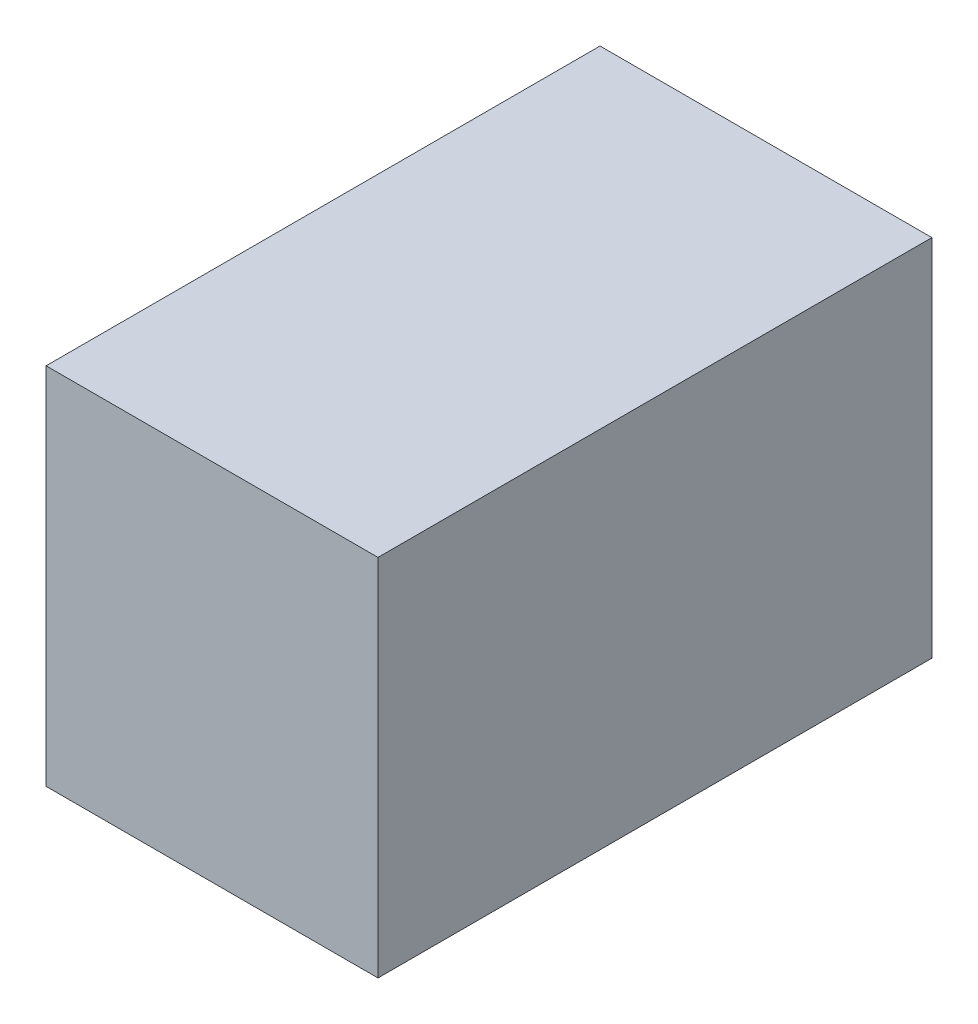
SolidWorks part; units mm, degrees
ref_plane "Front Plane" through (0, 0, 0) normal (0, 0, 1) x (1, 0, 0)
ref_plane "Top Plane" through (0, 0, 0) normal (0, 1, 0) x (1, 0, 0)
ref_plane "Right Plane" through (0, 0, 0) normal (1, 0, 0) x (0, 0, -1)
sketch "Sketch4" plane through (0, 0, 0) normal (1, 0, 0) x (0, 0, -1)
  line L1 (-15.525, 9.525) -> (15.525, 9.525)
  line L2 (-15.525, 9.525) -> (-15.525, -9.525)
  line L3 (-15.525, -9.525) -> (15.525, -9.525)
  line L4 (15.525, 9.525) -> (15.525, -9.525)
  line L5 (-15.525, 9.525) -> (15.525, -9.525) construction
  line L6 (-15.525, -9.525) -> (15.525, 9.525) construction
  point P0 (0, 0)
  dimension "D1" = 31.05
  dimension "D2" = 19.05
extrude "Boss-Extrude1" add sketch "Sketch4" along normal blind 19
shell "Shell1" thickness 2
sketch "Sketch5" plane through (0, 0, -17.525) normal (0, 0, -1) x (-1, 0, 0)
  line L0 (0, -11.525) -> (0, 11.525) construction
  line L1 (0, 9.525) -> (-12, 9.525)
  line L2 (-12, 9.525) -> (-12, -9.525)
  line L3 (-12, -9.525) -> (0, -9.525)
  line L4 (-21, 11.525) -> (0, 11.525) construction
  line L5 (-21, -11.525) -> (0, -11.525) construction
  line L6 (0, 9.525) -> (0, -9.525)
  dimension "D1" = 12
  dimension "D2" = 2
  dimension "D3" = 2
extrude "Cut-Extrude1" cut sketch "Sketch5" against normal up to surface (2 mm away) up to face at (9.5, 0, -15.525)
equation "\"terminalRad\"= 3mm"
equation "\"terminalLen\"= 10.5mm"
equation "\"threadlen\"=11"
